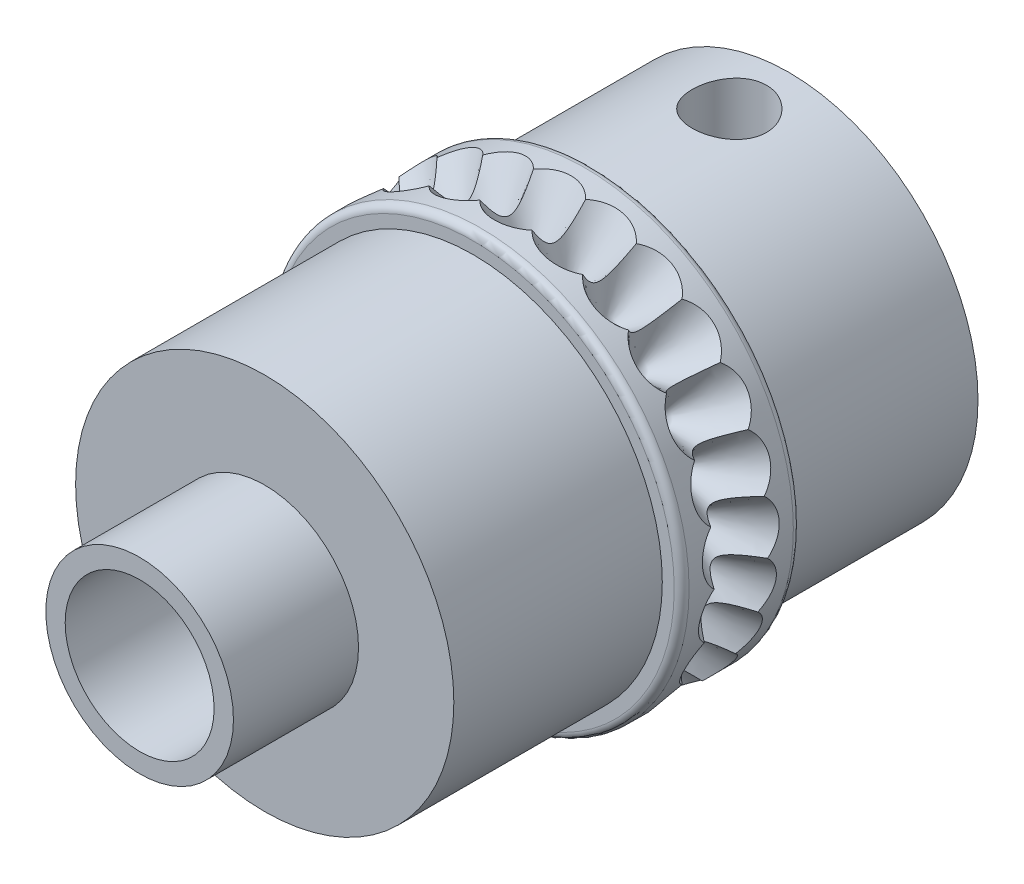
SolidWorks part; units mm, degrees
material "Stainless Steel (ferritic)"
ref_plane "Front Plane" through (0, 0, 0) normal (0, 0, 1) x (1, 0, 0)
ref_plane "Top Plane" through (0, 0, 0) normal (0, 1, 0) x (1, 0, 0)
ref_plane "Right Plane" through (0, 0, 0) normal (1, 0, 0) x (0, 0, -1)
sketch "Sketch1" plane through (0, 0, 0) normal (0, 0, 1) x (1, 0, 0)
  circle A0 centre (0, 0) radius 7.5
  circle A1 centre (0, 0) radius 2.5
  dimension "D1" = 15
  dimension "D2" = 5
extrude "Boss-Extrude1" add sketch "Sketch1" along normal mid plane 4
sketch "Sketch2" plane through (0, 0, 0) normal (1, 0, 0) x (0, 0, -1)
  line L0 (0, 0.195) -> (0, 7.7989) construction
  line L1 (0, 4.77) -> (1.7874, 7.8658)
  line L2 (2, -7.5) -> (2, 7.5) construction
  line L3 (1.7874, 7.8658) -> (0, 7.8658)
  line L4 (0, 7.8658) -> (0, 4.77)
  dimension "D1" = 4.77
revolve "Cut-Revolve2" cut sketch "Sketch2" angle 360 about L0
pattern_circular "CirPattern1" [suppressed] count 20 over 360
sketch "Sketch3" plane through (0, 0, -2) normal (0, 0, -1) x (-1, 0, 0)
  circle A0 centre (0, 0) radius 6.35
  circle A1 centre (0, 0) radius 2.5 construction
  circle A2 centre (0, 0) radius 2.5
  dimension "D1" = 12.7
extrude "Boss-Extrude2" add sketch "Sketch3" along normal blind 7.1
hole_wizard "M3 Tapped Hole1" positions "Sketch6" profile "Sketch7" tap size "M3" standard "ISO"
sketch "Sketch6" plane through (0, 0, 0) normal (0, 1, 0) x (1, 0, 0)
  line L0 (2.5, 9.1) -> (-2.5, 9.1) construction
  point P0 (0, 6.6)
  dimension "D1" = 2.5
sketch "Sketch7" plane through (0, 0, -6.6) normal (1, 0, 0) x (0, 0, -1)
  line L0 (0, 0) -> (0, 7.5)
  line L1 (0, 7.5) -> (1.25, 7.5)
  line L2 (1.25, 7.5) -> (1.25, 0)
  line L5 (1.25, 0) -> (0, 0)
  line L11 (0, -6.35) -> (0, 107.95) construction
  dimension "Thru Tap Drill Dia." = 2.5
  dimension "Thru Tap Drill Depth" = 7.5
cosmetic thread "Hole Thread1" parameters "D2"=3
pattern_circular "CirPattern2" [suppressed] count 50 over 360
pattern_circular "CirPattern3" [suppressed] count 60 over 360
pattern_circular "CirPattern4" [suppressed] count 30 over 360
pattern_circular "CirPattern5" count 25 over 360 about axis through (0, 0, -9.1) along (0, 0, 1) of "Cut-Revolve2"
sketch "Sketch9" plane through (0, 0, 2) normal (0, 0, 1) x (1, 0, 0)
  circle A0 centre (0, 0) radius 7
  circle A1 centre (0, 0) radius 9.5956
  dimension "D1" = 14
extrude "Cut-Extrude1" cut sketch "Sketch9" against normal through all
sketch "Sketch10" plane through (0, 0, -9.1) normal (0, 0, -1) x (-1, 0, 0)
  circle A0 centre (0, 0) radius 3.25
  circle A1 centre (0, 0) radius 6.35
  dimension "D1" = 6.5
extrude "Cut-Extrude2" cut sketch "Sketch10" against normal blind 0.5
sketch "Sketch11" plane through (0, 0, 2) normal (0, 0, 1) x (1, 0, 0)
  circle A0 centre (0, 0) radius 3.15
  circle A1 centre (0, 0) radius 2.5
  dimension "D1" = 6.3
extrude "Boss-Extrude3" add sketch "Sketch11" along normal blind 11.2
sketch "Sketch12" plane through (0, 0, 2) normal (0, 0, 1) x (1, 0, 0)
  circle A0 centre (0, 0) radius 6.35
  circle A1 centre (0, 0) radius 6.35 construction
  circle A2 centre (0, 0) radius 3.15 construction
  circle A3 centre (0, 0) radius 3.15
extrude "Boss-Extrude4" add sketch "Sketch12" along normal blind 7
fillet "Fillet1" radius 0.25 2 edges at (7, 0, -2) (7, 0, 2)
